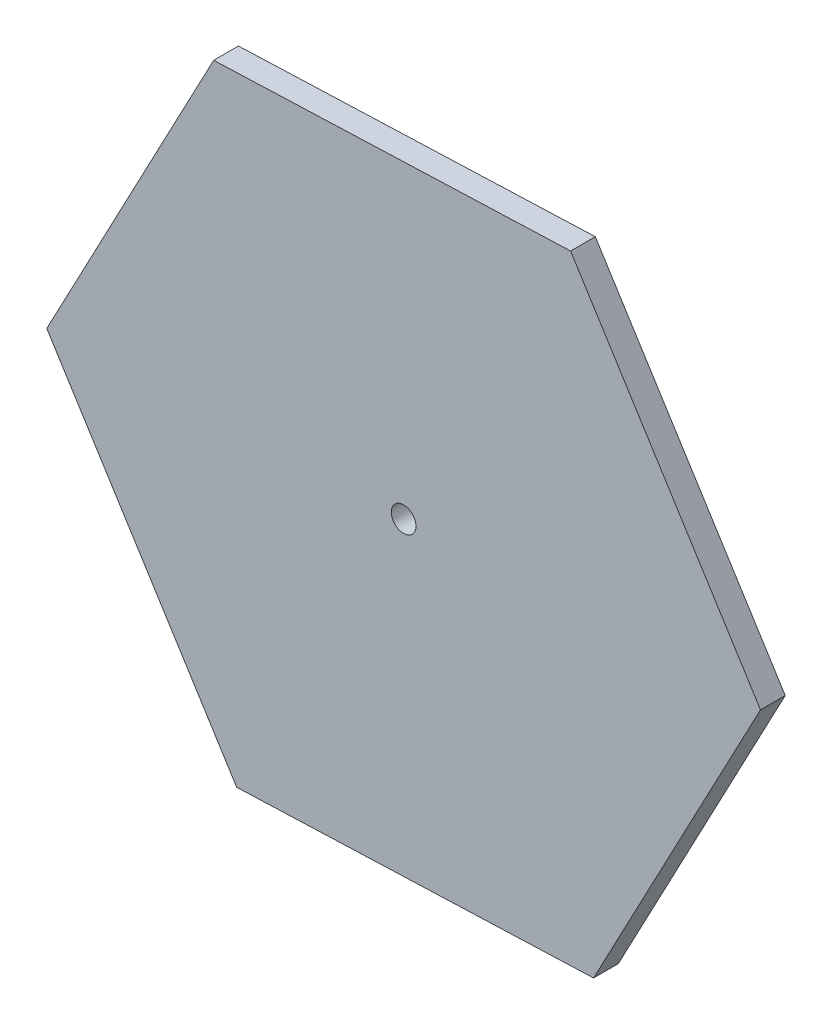
SolidWorks part; units mm, degrees
ref_plane "Front Plane" through (0, 0, 0) normal (0, 0, 1) x (1, 0, 0)
ref_plane "Top Plane" through (0, 0, 0) normal (0, 1, 0) x (1, 0, 0)
ref_plane "Right Plane" through (0, 0, 0) normal (1, 0, 0) x (0, 0, -1)
sketch "Sketch1" plane through (0, 0, 0) normal (0, 0, 1) x (1, 0, 0)
  line L1 (153.5311, -244.4617) -> (288.4756, 10.731)
  line L2 (288.4756, 10.731) -> (134.9445, 255.1927)
  line L3 (134.9445, 255.1927) -> (-153.5311, 244.4617)
  line L4 (-153.5311, 244.4617) -> (-288.4756, -10.731)
  line L5 (-288.4756, -10.731) -> (-134.9445, -255.1927)
  line L6 (-134.9445, -255.1927) -> (153.5311, -244.4617)
  circle A0 centre (0, 0) radius 250 construction
extrude "Boss-Extrude1" add sketch "Sketch1" along normal blind 20
sketch "Sketch2" plane through (0, 0, 20) normal (0, 0, 1) x (1, 0, 0)
  circle A0 centre (0, 0) radius 10
extrude "Cut-Extrude1" cut sketch "Sketch2" against normal blind 20
